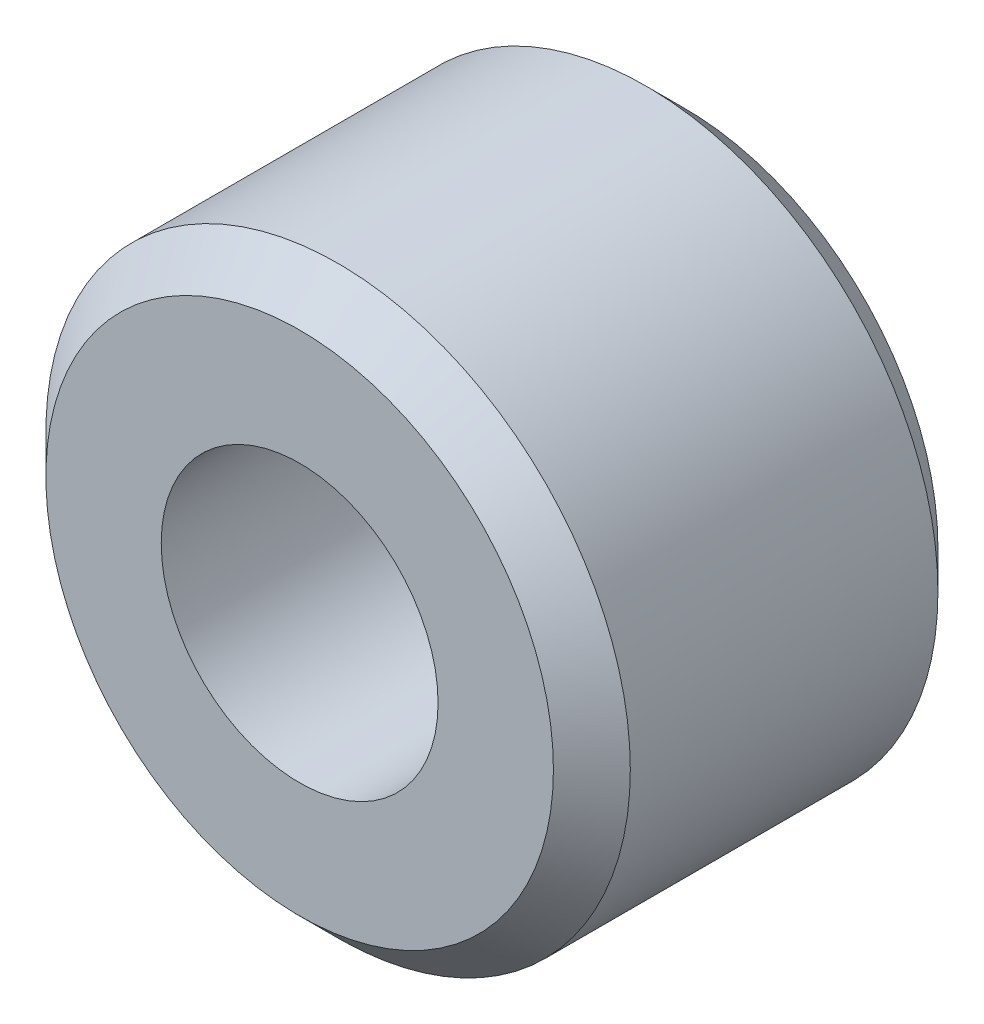
SolidWorks part; units mm, degrees
ref_plane "Front Plane" through (0, 0, 0) normal (0, 0, 1) x (1, 0, 0)
ref_plane "Top Plane" through (0, 0, 0) normal (0, 1, 0) x (1, 0, 0)
ref_plane "Right Plane" through (0, 0, 0) normal (1, 0, 0) x (0, 0, -1)
sketch "Sketch1" plane through (0, 0, 0) normal (0, 0, 1) x (1, 0, 0)
  circle A0 centre (0, 0) radius 1.8
  circle A1 centre (0, 0) radius 3.8
  dimension "D1" = 3.6
  dimension "D2" = 2
extrude "Boss-Extrude1" add sketch "Sketch1" along normal blind 5
chamfer "Chamfer1" distance 0.5 angle 45 2 edges at (3.8, 0, 0) (3.8, 0, 5)
